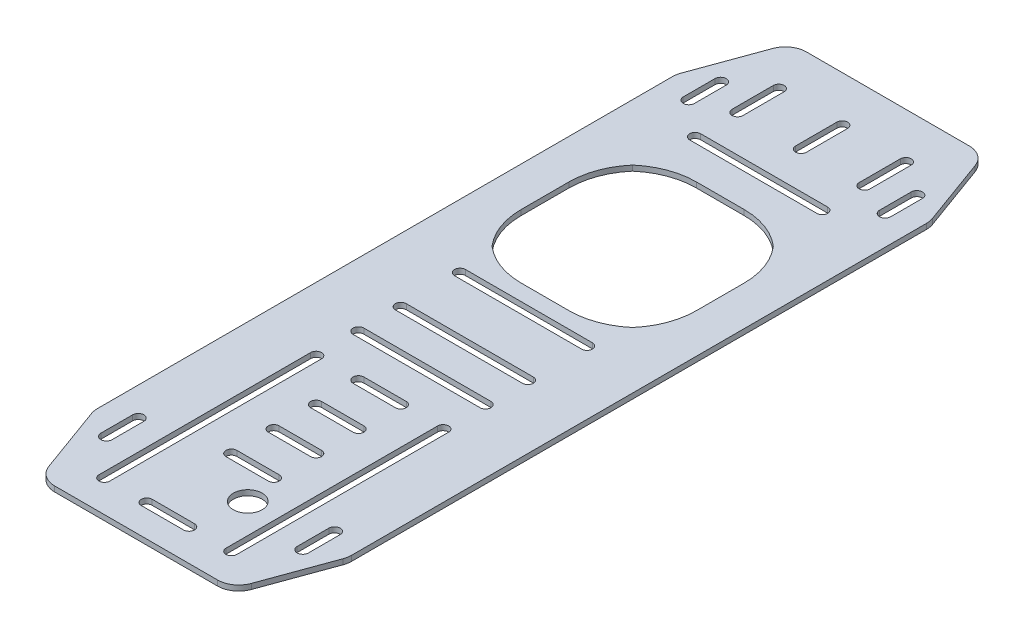
SolidWorks part; units mm, degrees
material "6061-T6 (SS)"
ref_plane "Front Plane" through (0, 0, 0) normal (0, 0, 1) x (1, 0, 0)
ref_plane "Top Plane" through (0, 0, 0) normal (0, 1, 0) x (1, 0, 0)
ref_plane "Right Plane" through (0, 0, 0) normal (1, 0, 0) x (0, 0, -1)
sketch "Sketch1" plane through (0, 0, 0) normal (0, 1, 0) x (1, 0, 0)
  line L0 (0, 495.0997) -> (0, -495.0997) construction
  line L8 (76.2, 330.2) -> (-76.2, 330.2)
  line L9 (76.2, 330.2) -> (76.2, -330.2)
  line L10 (76.2, -330.2) -> (-76.2, -330.2)
  line L11 (-76.2, 330.2) -> (-76.2, -330.2)
  line L12 (76.2, 330.2) -> (-76.2, -330.2) construction
  line L13 (76.2, -330.2) -> (-76.2, 330.2) construction
  point P7 (0, 0)
  dimension "D1" = 660.4
  dimension "D2" = 152.4
extrude "Boss-Extrude1" add sketch "Sketch1" along normal blind 3.18
sketch "Sketch5" plane through (0, 0, 0) normal (0, -1, 0) x (1, 0, 0)
  line L0 (76.2, 279.4) -> (57.7103, 330.2)
  line L1 (76.2, 330.2) -> (76.2, -330.2) construction
  line L2 (-76.2, 330.2) -> (76.2, 330.2) construction
  line L3 (57.7103, 330.2) -> (76.2, 330.2)
  line L4 (76.2, 330.2) -> (76.2, 279.4)
  line L5 (0, -1.749) -> (0, 1.749) construction
  line L6 (-57.7103, 330.2) -> (-76.2, 330.2)
  line L7 (-76.2, 279.4) -> (-57.7103, 330.2)
  line L8 (-76.2, 330.2) -> (-76.2, 279.4)
  line L9 (1.749, 0) -> (-1.749, 0) construction
  line L10 (-76.2, -279.4) -> (-57.7103, -330.2)
  line L11 (-76.2, -330.2) -> (-76.2, -279.4)
  line L12 (-57.7103, -330.2) -> (-76.2, -330.2)
  line L13 (57.7103, -330.2) -> (76.2, -330.2)
  line L14 (76.2, -279.4) -> (57.7103, -330.2)
  line L15 (76.2, -330.2) -> (76.2, -279.4)
  dimension "D1" = 20
  dimension "D2" = 50.8
sketch "Sketch3" plane through (0, 3.18, 0) normal (0, 1, 0) x (1, 0, 0)
  line L0 (-38.1, -101.6) -> (38.1, -101.6) construction
  line L1 (-76.2, -330.2) -> (76.2, -330.2) construction
  line L2 (-38.1, 50.8) -> (38.1, 50.8) construction
  line L5 (-38.1, 54.0639) -> (38.1, 54.0639)
  line L9 (-38.1, 47.5361) -> (38.1, 47.5361)
  line L12 (-76.2, 0) -> (76.2, 0) construction
  line L13 (-76.2, 330.2) -> (-76.2, -330.2) construction
  line L14 (76.2, -330.2) -> (76.2, 330.2) construction
  line L15 (-38.1, 25.4) -> (-38.1, -101.6) construction
  line L16 (-41.3639, 25.4) -> (-41.3639, -101.6)
  line L17 (-34.8361, 25.4) -> (-34.8361, -101.6)
  line L18 (38.1, 25.4) -> (38.1, -101.6) construction
  line L19 (41.3639, 25.4) -> (41.3639, -101.6)
  line L20 (34.8361, 25.4) -> (34.8361, -101.6)
  line L21 (-76.2, -38.1) -> (76.2, -38.1) construction
  line L22 (-76.2, 330.2) -> (-76.2, -330.2) construction
  line L23 (76.2, -330.2) -> (76.2, 330.2) construction
  line L24 (-38.1, -127) -> (38.1, -127) construction
  line L25 (-38.1, -130.2639) -> (38.1, -130.2639)
  line L26 (-38.1, -123.7361) -> (38.1, -123.7361)
  line L27 (-76.2, -127) -> (76.2, -127) construction
  line L28 (38.1, -279.4) -> (38.1, -152.4) construction
  line L29 (41.3639, -279.4) -> (41.3639, -152.4)
  line L30 (34.8361, -279.4) -> (34.8361, -152.4)
  line L31 (-38.1, -279.4) -> (-38.1, -152.4) construction
  line L32 (-41.3639, -279.4) -> (-41.3639, -152.4)
  line L33 (-34.8361, -279.4) -> (-34.8361, -152.4)
  line L34 (-76.2, -215.9) -> (76.2, -215.9) construction
  line L35 (-38.1, -304.8) -> (38.1, -304.8) construction
  line L36 (-38.1, -301.5361) -> (38.1, -301.5361)
  line L37 (-38.1, -308.0639) -> (38.1, -308.0639)
  line L38 (-12.7, -279.4) -> (12.7, -279.4) construction
  line L39 (-12.7, -276.1361) -> (12.7, -276.1361)
  line L40 (-12.7, -282.6639) -> (12.7, -282.6639)
  line L44 (-12.7, -228.6) -> (12.7, -228.6) construction
  line L45 (-12.7, -225.3361) -> (12.7, -225.3361)
  line L46 (-12.7, -231.8639) -> (12.7, -231.8639)
  line L47 (-12.7, -203.2) -> (12.7, -203.2) construction
  line L48 (-12.7, -199.9361) -> (12.7, -199.9361)
  line L49 (-12.7, -206.4639) -> (12.7, -206.4639)
  line L50 (-12.7, -177.8) -> (12.7, -177.8) construction
  line L51 (-12.7, -174.5361) -> (12.7, -174.5361)
  line L52 (-12.7, -181.0639) -> (12.7, -181.0639)
  line L53 (-12.7, -152.4) -> (12.7, -152.4) construction
  line L54 (-12.7, -149.1361) -> (12.7, -149.1361)
  line L55 (-12.7, -155.6639) -> (12.7, -155.6639)
  line L56 (-12.7, 25.4) -> (12.7, 25.4) construction
  line L57 (-12.7, 22.1361) -> (12.7, 22.1361)
  line L58 (-12.7, 28.6639) -> (12.7, 28.6639)
  line L59 (-12.7, 0) -> (12.7, 0) construction
  line L60 (-12.7, -3.2639) -> (12.7, -3.2639)
  line L61 (-12.7, 3.2639) -> (12.7, 3.2639)
  line L62 (-12.7, -25.4) -> (12.7, -25.4) construction
  line L63 (-12.7, -28.6639) -> (12.7, -28.6639)
  line L64 (-12.7, -22.1361) -> (12.7, -22.1361)
  line L65 (-12.7, -50.8) -> (12.7, -50.8) construction
  line L66 (-12.7, -54.0639) -> (12.7, -54.0639)
  line L67 (-12.7, -47.5361) -> (12.7, -47.5361)
  line L71 (-12.7, -101.6) -> (12.7, -101.6) construction
  line L72 (-12.7, -104.8639) -> (12.7, -104.8639)
  line L73 (-12.7, -98.3361) -> (12.7, -98.3361)
  line L74 (-76.2, 63.5) -> (76.2, 63.5) construction
  line L75 (-38.1, 76.2) -> (38.1, 76.2) construction
  line L76 (-38.1, 72.9361) -> (38.1, 72.9361)
  line L77 (-38.1, 79.4639) -> (38.1, 79.4639)
  line L78 (-76.2, 151.7678) -> (76.2, 151.7678) construction
  line L79 (76.2, 330.2) -> (-76.2, 330.2) construction
  line L80 (-38.1, 207.0156) -> (38.1, 207.0156) construction
  line L83 (-38.1, 252.7356) -> (38.1, 252.7356) construction
  line L84 (-38.1, 249.4717) -> (38.1, 249.4717)
  line L85 (-38.1, 255.9995) -> (38.1, 255.9995)
  line L86 (-38.1, 302.8393) -> (-38.1, 278.1356) construction
  line L87 (-34.8361, 302.8393) -> (-34.8361, 278.1356)
  line L88 (-41.3639, 302.8393) -> (-41.3639, 278.1356)
  line L89 (0, 302.8393) -> (0, 278.1356) construction
  line L90 (3.2639, 302.8393) -> (3.2639, 278.1356)
  line L91 (-3.2639, 302.8393) -> (-3.2639, 278.1356)
  line L92 (38.1, 302.8393) -> (38.1, 278.1356) construction
  line L93 (41.3639, 302.8393) -> (41.3639, 278.1356)
  line L94 (34.8361, 302.8393) -> (34.8361, 278.1356)
  line L95 (-38.1, 203.7517) -> (38.1, 203.7517)
  line L96 (-38.1, 210.2795) -> (38.1, 210.2795)
  line L97 (76.2, 330.2) -> (-76.2, 330.2) construction
  line L107 (-12.7, -254) -> (12.7, -254) construction
  line L108 (-12.7, -250.7361) -> (12.7, -250.7361)
  line L109 (-12.7, -257.2639) -> (12.7, -257.2639)
  line L110 (-12.7, -254) -> (12.7, -254) construction
  line L111 (-12.7, -250.7361) -> (12.7, -250.7361)
  line L112 (-12.7, -257.2639) -> (12.7, -257.2639)
  arc A4 (-41.3639, 25.4) -> (-34.8361, 25.4) centre (-38.1, 25.4) cw
  arc A5 (-34.8361, -101.6) -> (-41.3639, -101.6) centre (-38.1, -101.6) cw
  arc A6 (41.3639, 25.4) -> (34.8361, 25.4) centre (38.1, 25.4) ccw
  arc A7 (34.8361, -101.6) -> (41.3639, -101.6) centre (38.1, -101.6) ccw
  arc A8 (-38.1, 54.0639) -> (-38.1, 47.5361) centre (-38.1, 50.8) ccw
  arc A9 (38.1, 47.5361) -> (38.1, 54.0639) centre (38.1, 50.8) ccw
  arc A10 (-38.1, -130.2639) -> (-38.1, -123.7361) centre (-38.1, -127) cw
  arc A11 (38.1, -123.7361) -> (38.1, -130.2639) centre (38.1, -127) cw
  arc A12 (41.3639, -279.4) -> (34.8361, -279.4) centre (38.1, -279.4) cw
  arc A13 (34.8361, -152.4) -> (41.3639, -152.4) centre (38.1, -152.4) cw
  arc A14 (-41.3639, -279.4) -> (-34.8361, -279.4) centre (-38.1, -279.4) ccw
  arc A15 (-34.8361, -152.4) -> (-41.3639, -152.4) centre (-38.1, -152.4) ccw
  arc A16 (-38.1, -301.5361) -> (-38.1, -308.0639) centre (-38.1, -304.8) ccw
  arc A17 (38.1, -308.0639) -> (38.1, -301.5361) centre (38.1, -304.8) ccw
  arc A18 (-12.7, -276.1361) -> (-12.7, -282.6639) centre (-12.7, -279.4) ccw
  arc A19 (12.7, -282.6639) -> (12.7, -276.1361) centre (12.7, -279.4) ccw
  arc A22 (-12.7, -225.3361) -> (-12.7, -231.8639) centre (-12.7, -228.6) ccw
  arc A23 (12.7, -231.8639) -> (12.7, -225.3361) centre (12.7, -228.6) ccw
  arc A24 (-12.7, -199.9361) -> (-12.7, -206.4639) centre (-12.7, -203.2) ccw
  arc A25 (12.7, -206.4639) -> (12.7, -199.9361) centre (12.7, -203.2) ccw
  arc A26 (-12.7, -174.5361) -> (-12.7, -181.0639) centre (-12.7, -177.8) ccw
  arc A27 (12.7, -181.0639) -> (12.7, -174.5361) centre (12.7, -177.8) ccw
  arc A28 (-12.7, -149.1361) -> (-12.7, -155.6639) centre (-12.7, -152.4) ccw
  arc A29 (12.7, -155.6639) -> (12.7, -149.1361) centre (12.7, -152.4) ccw
  arc A30 (-12.7, 22.1361) -> (-12.7, 28.6639) centre (-12.7, 25.4) cw
  arc A31 (12.7, 28.6639) -> (12.7, 22.1361) centre (12.7, 25.4) cw
  arc A32 (-12.7, -3.2639) -> (-12.7, 3.2639) centre (-12.7, 0) cw
  arc A33 (12.7, 3.2639) -> (12.7, -3.2639) centre (12.7, 0) cw
  arc A34 (-12.7, -28.6639) -> (-12.7, -22.1361) centre (-12.7, -25.4) cw
  arc A35 (12.7, -22.1361) -> (12.7, -28.6639) centre (12.7, -25.4) cw
  arc A36 (-12.7, -54.0639) -> (-12.7, -47.5361) centre (-12.7, -50.8) cw
  arc A37 (12.7, -47.5361) -> (12.7, -54.0639) centre (12.7, -50.8) cw
  arc A40 (-12.7, -104.8639) -> (-12.7, -98.3361) centre (-12.7, -101.6) cw
  arc A41 (12.7, -98.3361) -> (12.7, -104.8639) centre (12.7, -101.6) cw
  arc A42 (-38.1, 72.9361) -> (-38.1, 79.4639) centre (-38.1, 76.2) cw
  arc A43 (38.1, 79.4639) -> (38.1, 72.9361) centre (38.1, 76.2) cw
  arc A46 (-38.1, 249.4717) -> (-38.1, 255.9995) centre (-38.1, 252.7356) cw
  arc A47 (38.1, 255.9995) -> (38.1, 249.4717) centre (38.1, 252.7356) cw
  arc A48 (-34.8361, 302.8393) -> (-41.3639, 302.8393) centre (-38.1, 302.8393) ccw
  arc A49 (-41.3639, 278.1356) -> (-34.8361, 278.1356) centre (-38.1, 278.1356) ccw
  arc A50 (3.2639, 302.8393) -> (-3.2639, 302.8393) centre (0, 302.8393) ccw
  arc A51 (-3.2639, 278.1356) -> (3.2639, 278.1356) centre (0, 278.1356) ccw
  arc A52 (41.3639, 302.8393) -> (34.8361, 302.8393) centre (38.1, 302.8393) ccw
  arc A53 (34.8361, 278.1356) -> (41.3639, 278.1356) centre (38.1, 278.1356) ccw
  arc A54 (-38.1, 203.7517) -> (-38.1, 210.2795) centre (-38.1, 207.0156) cw
  arc A55 (38.1, 210.2795) -> (38.1, 203.7517) centre (38.1, 207.0156) cw
  arc A64 (-12.7, -250.7361) -> (-12.7, -257.2639) centre (-12.7, -254) ccw
  arc A65 (12.7, -257.2639) -> (12.7, -250.7361) centre (12.7, -254) ccw
  point P2 (0, 50.8)
  point P26 (0, -127)
  point P36 (-38.1, -38.1)
  point P43 (38.1, -38.1)
  point P55 (38.1, -215.9)
  point P62 (-38.1, -215.9)
  point P71 (0, -304.8)
  point P78 (0, -279.4)
  point P94 (0, -228.6)
  point P101 (0, -203.2)
  point P108 (0, -177.8)
  point P115 (0, -152.4)
  point P121 (0, 25.4)
  point P128 (0, 0)
  point P135 (0, -25.4)
  point P142 (0, -50.8)
  point P156 (0, -101.6)
  point P165 (0, 76.2)
  point P176 (0, 207.0156)
  point P177 (0, 207.0156)
  point P183 (0, 252.7356)
  point P190 (-38.1, 290.4874)
  point P197 (0, 290.4874)
  point P205 (38.1, 290.4874)
  point P212 (0, -254)
  point P221 (0, -254)
  point P228 (0, -254)
  point P235 (0, -254)
  point P242 (0, -254)
  dimension "D1" = 3.2639
  dimension "D2" = 76.2
  dimension "D5" = 3.2639
  dimension "D7" = 3.2639
  dimension "D14" = 3.2639
  dimension "D3" = 228.6
  dimension "D4" = 127
  dimension "D6" = 25.4
  dimension "D8" = 25.4
  dimension "D9" = 6
  dimension "D11" = 12.7
  dimension "D12" = 50.1037
  dimension "7.02489" = 178.4322
  dimension "D13" = 25.4
  dimension "D16" = 38.1
  dimension "D17" = 123.1844
  dimension "D15" = 3
extrude "Cut-Extrude2" cut sketch "Sketch3" against normal through all
sketch "Sketch4" plane through (0, 3.18, 0) normal (0, 1, 0) x (1, 0, 0)
  line L47 (-14.3614, 124.6113) -> (14.3614, 124.6113)
  line L48 (52.54, 162.7899) -> (52.54, 191.5127)
  line L49 (14.3614, 229.6913) -> (-14.3614, 229.6913)
  line L50 (-52.54, 191.5127) -> (-52.54, 162.7899)
  line L51 (-14.3614, 124.6113) -> (14.3614, 124.6113)
  line L52 (52.54, 162.7899) -> (52.54, 191.5127)
  line L53 (14.3614, 229.6913) -> (-14.3614, 229.6913)
  line L54 (-52.54, 191.5127) -> (-52.54, 162.7899)
  arc A93 (-42.1819, 134.9694) -> (-14.3614, 124.6113) centre (-14.3614, 167.1513) ccw
  arc A94 (14.3614, 124.6113) -> (42.1819, 134.9694) centre (14.3614, 167.1513) ccw
  arc A95 (42.1819, 134.9694) -> (52.54, 162.7899) centre (10, 162.7899) ccw
  arc A96 (52.54, 191.5127) -> (42.1819, 219.3332) centre (10, 191.5127) ccw
  arc A97 (42.1819, 219.3332) -> (14.3614, 229.6913) centre (14.3614, 187.1513) ccw
  arc A98 (-14.3614, 229.6913) -> (-42.1819, 219.3332) centre (-14.3614, 187.1513) ccw
  arc A99 (-42.1819, 219.3332) -> (-52.54, 191.5127) centre (-10, 191.5127) ccw
  arc A100 (-52.54, 162.7899) -> (-42.1819, 134.9694) centre (-10, 162.7899) ccw
  arc A101 (-42.1819, 134.9694) -> (-14.3614, 124.6113) centre (-14.3614, 167.1513) ccw
  arc A102 (14.3614, 124.6113) -> (42.1819, 134.9694) centre (14.3614, 167.1513) ccw
  arc A103 (42.1819, 134.9694) -> (52.54, 162.7899) centre (10, 162.7899) ccw
  arc A104 (52.54, 191.5127) -> (42.1819, 219.3332) centre (10, 191.5127) ccw
  arc A105 (42.1819, 219.3332) -> (14.3614, 229.6913) centre (14.3614, 187.1513) ccw
  arc A106 (-14.3614, 229.6913) -> (-42.1819, 219.3332) centre (-14.3614, 187.1513) ccw
  arc A107 (-42.1819, 219.3332) -> (-52.54, 191.5127) centre (-10, 191.5127) ccw
  arc A108 (-52.54, 162.7899) -> (-42.1819, 134.9694) centre (-10, 162.7899) ccw
  dimension "D1" = 2.54
extrude "Cut-Extrude3" cut sketch "Sketch4" against normal through all
extrude "Cut-Extrude4" cut sketch "Sketch5" against normal through all
fillet "Fillet1" radius 12.7 8 edges at (-76.2, 1.59, -279.4) (-57.7103, 1.59, -330.2) (57.7103, 1.59, -330.2) (76.2, 1.59, -279.4) (76.2, 1.59, 279.4) (57.7103, 1.59, 330.2) (-57.7103, 1.59, 330.2) (-76.2, 1.59, 279.4)
sketch "Sketch6" plane through (0, 3.18, 0) normal (0, 1, 0) x (1, 0, 0)
  circle A1 centre (17.106, -70.8034) radius 8.636 construction
  circle A2 centre (17.106, -70.8034) radius 8.636
sketch "Sketch7" plane through (0, 0, 0) normal (0, -1, 0) x (1, 0, 0)
  line L0 (76.2, 330.2) -> (76.2, 120.65)
  line L1 (76.2, 277.1606) -> (76.2, -277.1606) construction
  line L2 (76.2, 120.65) -> (-76.2, 120.65)
  line L3 (-76.2, 120.65) -> (-76.2, 330.2)
  line L4 (-76.2, -277.1606) -> (-76.2, 277.1606) construction
  line L5 (-76.2, 330.2) -> (76.2, 330.2)
  line L6 (-48.8177, 330.2) -> (48.8177, 330.2) construction
  dimension "D1" = 209.55
extrude "Cut-Extrude6" cut sketch "Sketch7" against normal up to next
sketch "Sketch8" plane through (0, 0, 0) normal (0, -1, 0) x (1, 0, 0)
  line L0 (76.2, 69.85) -> (76.2, 120.65)
  line L1 (76.2, 120.65) -> (76.2, -277.1606) construction
  line L2 (76.2, 120.65) -> (57.7103, 120.65)
  line L3 (-76.2, 120.65) -> (76.2, 120.65) construction
  line L4 (57.7103, 120.65) -> (76.2, 69.85)
  line L5 (0, -330.2) -> (0, 120.65) construction
  line L6 (48.8177, -330.2) -> (-48.8177, -330.2) construction
  line L7 (-76.2, 120.65) -> (-57.7103, 120.65)
  line L8 (-76.2, 69.85) -> (-76.2, 120.65)
  line L9 (-57.7103, 120.65) -> (-76.2, 69.85)
  dimension "D1" = 50.8
  dimension "D2" = 20
extrude "Cut-Extrude7" cut sketch "Sketch8" against normal up to next
fillet "Fillet2" radius 12.7 4 edges at (57.7103, 1.59, 120.65) (76.2, 1.59, 69.85) (-57.7103, 1.59, 120.65) (-76.2, 1.59, 69.85)
sketch "Sketch9" plane through (0, 0, 0) normal (0, -1, 0) x (1, 0, 0)
  line L0 (58.674, -269.875) -> (58.674, -288.925) construction
  line L1 (62.0522, -269.875) -> (62.0522, -288.925)
  line L2 (55.2958, -269.875) -> (55.2958, -288.925)
  line L3 (-59.0358, -269.875) -> (-59.0358, -288.925) construction
  line L4 (-55.6576, -269.875) -> (-55.6576, -288.925)
  line L5 (-62.414, -269.875) -> (-62.414, -288.925)
  line L6 (76.2, -104.775) -> (-76.2, -104.775) construction
  line L7 (76.2, 67.6106) -> (76.2, -277.1606) construction
  line L8 (-76.2, -277.1606) -> (-76.2, 67.6106) construction
  line L9 (-59.0358, 60.325) -> (-59.0358, 79.375) construction
  line L12 (-55.6576, 60.325) -> (-55.6576, 79.375)
  line L15 (58.674, -279.4) -> (-59.0358, -279.4) construction
  line L16 (48.8177, -330.2) -> (-48.8177, -330.2) construction
  line L17 (-62.414, 60.325) -> (-62.414, 79.375)
  line L18 (58.674, 60.325) -> (58.674, 79.375) construction
  line L19 (62.0522, 60.325) -> (62.0522, 79.375)
  line L20 (55.2958, 60.325) -> (55.2958, 79.375)
  arc A0 (62.0522, -269.875) -> (55.2958, -269.875) centre (58.674, -269.875) ccw
  arc A1 (55.2958, -288.925) -> (62.0522, -288.925) centre (58.674, -288.925) ccw
  arc A2 (-55.6576, 60.325) -> (-62.414, 60.325) centre (-59.0358, 60.325) cw
  arc A3 (-55.6576, -269.875) -> (-62.414, -269.875) centre (-59.0358, -269.875) ccw
  arc A4 (-62.414, -288.925) -> (-55.6576, -288.925) centre (-59.0358, -288.925) ccw
  arc A5 (-62.414, 79.375) -> (-55.6576, 79.375) centre (-59.0358, 79.375) cw
  arc A10 (62.0522, 60.325) -> (55.2958, 60.325) centre (58.674, 60.325) cw
  arc A11 (55.2958, 79.375) -> (62.0522, 79.375) centre (58.674, 79.375) cw
  point P3 (58.674, -279.4)
  point P13 (-59.0358, -279.4)
  point P27 (-59.0358, 69.85)
  point P34 (58.674, 69.85)
  dimension "D2" = 3.3782
  dimension "D1" = 19.05
  dimension "D3" = 50.8
  dimension "D4" = 17.1642
  dimension "D5" = 17.526
extrude "Cut-Extrude8" cut sketch "Sketch9" against normal up to next
extrude "Cut-Extrude9" cut sketch "Sketch6" against normal through all
sketch "Sketch10" plane through (0, 0, 0) normal (0, -1, 0) x (1, 0, 0)
  line L0 (-38.1, -252.7356) -> (-38.1, -103.0796) construction
  line L3 (38.1, -252.7356) -> (38.1, -103.0796) construction
  line L4 (-38.1, -111.6954) -> (38.1, -111.6954) construction
  line L5 (-38.1, -111.6954) -> (38.1, -111.6954) construction
  line L6 (-38.1, -108.4315) -> (38.1, -108.4315)
  line L7 (-38.1, -114.9593) -> (38.1, -114.9593)
  line L8 (-14.3614, -124.6113) -> (14.3614, -124.6113) construction
  arc A2 (-38.1, -108.4315) -> (-38.1, -114.9593) centre (-38.1, -111.6954) ccw
  arc A3 (38.1, -114.9593) -> (38.1, -108.4315) centre (38.1, -111.6954) ccw
  arc A4 (-38.1, -249.4717) -> (-38.1, -255.9995) centre (-38.1, -252.7356) ccw construction
  point P4 (-0.038, -111.6954)
  point P9 (0, -111.6954)
  dimension "D1" = 9.652
extrude "Cut-Extrude10" cut sketch "Sketch10" against normal through all
